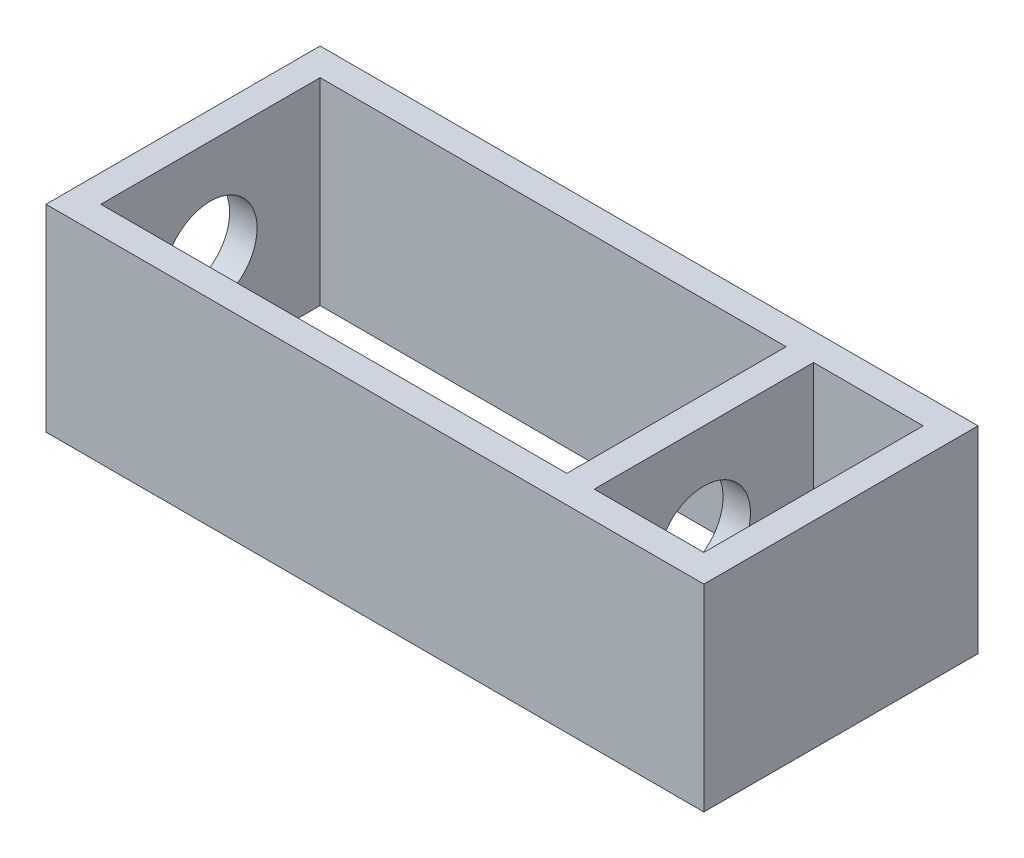
SolidWorks part; units mm, degrees
ref_plane "Front Plane" through (0, 0, 0) normal (0, 0, 1) x (1, 0, 0)
ref_plane "Top Plane" through (0, 0, 0) normal (0, 1, 0) x (1, 0, 0)
ref_plane "Right Plane" through (0, 0, 0) normal (1, 0, 0) x (0, 0, -1)
sketch "Sketch1" plane through (0, 0, 0) normal (0, 1, 0) x (1, 0, 0)
  line L0 (30, 0) -> (22.5, 0) construction
  line L1 (-22.5, -12.5) -> (37.5, -12.5)
  line L2 (37.5, -12.5) -> (-22.5, 12.5) construction
  line L3 (-22.5, 12.5) -> (37.5, 12.5)
  line L4 (-22.5, -12.5) -> (-22.5, 12.5)
  line L5 (37.5, 12.5) -> (-22.5, -12.5) construction
  line L6 (7.5, 0) -> (0, 0) construction
  line L7 (22.5, -10) -> (-20, -10)
  line L8 (22.5, -10) -> (22.5, 10)
  line L9 (22.5, 10) -> (-20, 10)
  line L10 (-20, -10) -> (-20, 10)
  line L11 (7.5, 0) -> (22.5, 0) construction
  line L13 (35, -10) -> (25, -10)
  line L15 (37.5, -12.5) -> (37.5, 12.5)
  line L17 (35, -10) -> (35, 10)
  line L20 (35, 10) -> (25, 10)
  line L21 (25, -10) -> (25, 10)
  line L22 (35, -10) -> (25, 10) construction
  line L23 (35, 10) -> (25, -10) construction
  point P0 (0, 0)
  point P6 (0, 0)
  dimension "D1" = 60
  dimension "D2" = 25
  dimension "D3" = 20
  dimension "D4" = 2.5
  dimension "D6" = 2.5
  dimension "D7" = 10
  dimension "D8" = 2.5
  dimension "D9" = 7.5
extrude "Boss-Extrude1" add sketch "Sketch1" along normal blind 18
sketch "Sketch3" plane through (-22.5, 0, 0) normal (-1, 0, 0) x (0, 0, 1)
  line L0 (-12.5, 18) -> (12.5, 0) construction
  line L1 (12.5, 18) -> (-12.5, 0) construction
  circle A0 centre (0, 9) radius 4.25
  dimension "D1" = 8.5
extrude "Cut-Extrude1" cut sketch "Sketch3" against normal up to surface (47.5 mm away) up to face at (25, 9, 0)
